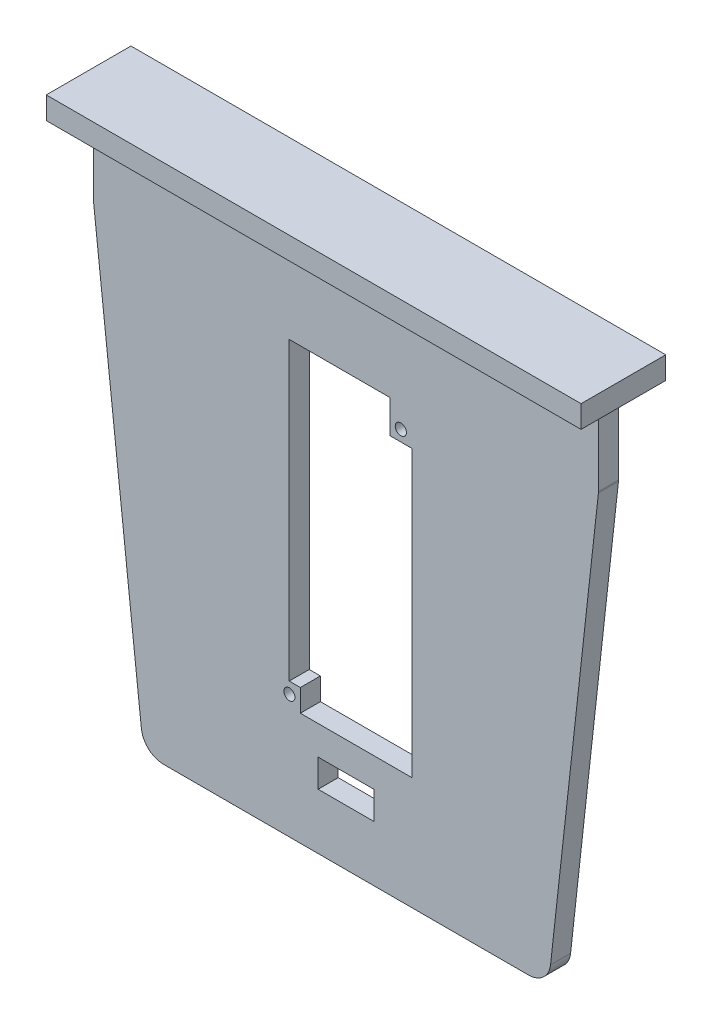
SolidWorks part; units mm, degrees
ref_plane "Front Plane" through (0, 0, 0) normal (0, 0, 1) x (1, 0, 0)
ref_plane "Top Plane" through (0, 0, 0) normal (0, 1, 0) x (1, 0, 0)
ref_plane "Right Plane" through (0, 0, 0) normal (1, 0, 0) x (0, 0, -1)
sketch "Sketch2" plane through (0, 0, 0) normal (0, 0, -1) x (-1, 0, 0)
  line L0 (-4.9216, 54.5793) -> (-4.9216, -59.013) construction
  line L6 (-62.4874, 48.8485) -> (52.6441, 48.8485)
  line L7 (52.6441, 48.8485) -> (41.7132, -49.932)
  line L8 (36.664, -54.4533) -> (-46.5073, -54.4533)
  line L9 (-62.4874, 48.8485) -> (-51.5564, -49.932)
  arc A4 (41.7132, -49.932) -> (36.664, -54.4533) centre (36.664, -49.3733) cw
  arc A5 (-51.5564, -49.932) -> (-46.5073, -54.4533) centre (-46.5073, -49.3733) ccw
  point P27 (-4.9216, -54.4533)
  point P28 (-4.9216, 48.8485)
  dimension "D4" = 98.7805
  dimension "D6" = 48.8485
  dimension "D11" = 5.08
  dimension "D2" = 115.1315
  dimension "D3" = 83.1712
  dimension "D5" = 36.664
extrude "Boss-Extrude1" add sketch "Sketch2" along normal blind 4.572
sketch "Sketch3" plane through (0, 48.8485, 0) normal (0, 1, 0) x (1, 0, 0)
  line L0 (-52.6441, 4.572) -> (-52.6441, 0)
  line L1 (-52.6441, 4.572) -> (62.4874, 4.572)
  line L2 (-52.6441, 0) -> (62.4874, 0)
  line L3 (62.4874, 4.572) -> (62.4874, 0)
  line L4 (62.4874, 4.572) -> (62.4874, 0) construction
  dimension "D1" = 0
extrude "Boss-Extrude2" add sketch "Sketch3" along normal blind 17.78
sketch "Sketch4" plane through (0, 66.6285, 0) normal (0, 1, 0) x (1, 0, 0)
  line L0 (-52.6441, 0) -> (62.4874, 0) construction
  line L1 (62.4874, 0) -> (62.4874, 4.572) construction
  line L2 (-52.6441, 0) -> (62.4874, 0) construction
  line L3 (62.4874, -7.366) -> (62.4874, 11.938) construction
  line L4 (-52.6441, -7.366) -> (-52.6441, 37.8542) construction
  line L5 (0, -33.6753) -> (0, 37.8542) construction
  line L10 (-56.0384, 11.938) -> (-56.0384, -7.366)
  line L11 (-56.0384, 11.938) -> (82.2468, 11.938) construction
  line L12 (62.4874, -7.366) -> (-56.0384, -7.366) construction
  line L13 (-56.0384, 11.938) -> (65.8816, 11.938)
  line L14 (-56.0384, -7.366) -> (65.8816, -7.366)
  line L15 (65.8816, 11.938) -> (65.8816, -7.366)
  line L16 (62.4874, 4.572) -> (-52.6441, 4.572) construction
  dimension "D1" = 7.366
  dimension "D2" = 7.366
  dimension "D3" = 3.3942
  dimension "D4" = 3.3942
fillet "Fillet1" radius 2.54 2 edges at (62.4874, 48.8485, -2.286) (-52.6441, 48.8485, -2.286)
extrude "Boss-Extrude4" add sketch "Sketch4" along normal blind 5.08
sketch "Sketch5" plane through (0, 0, -4.572) normal (0, 0, -1) x (-1, 0, 0)
  line L0 (-4.9216, 66.6285) -> (-4.9216, -54.4533) construction
  line L2 (-65.8816, 66.6285) -> (56.0384, 66.6285) construction
  line L3 (-46.5073, -54.4533) -> (36.664, -54.4533) construction
  line L4 (1.4284, -35.4033) -> (-11.2716, -35.4033)
  line L5 (-11.2716, -35.4033) -> (-11.2716, -41.7533)
  line L6 (-11.2716, -41.7533) -> (1.4284, -41.7533)
  line L7 (1.4284, -35.4033) -> (1.4284, -41.7533)
  point P11 (-4.9216, -41.7533)
  point P12 (-4.9216, -35.4033)
  dimension "D1" = 6.35
  dimension "D2" = 6.35
  dimension "D3" = 12.7
extrude "Cut-Extrude1" cut sketch "Sketch5" against normal blind 5.08
sketch "Sketch6" plane through (0, 0, -4.572) normal (0, 0, -1) x (-1, 0, 0)
  line L0 (-62.4874, 66.6285) -> (-62.4874, 48.9886) construction
  line L1 (-65.8816, 66.6285) -> (56.0384, 66.6285) construction
  line L2 (-11.2716, -41.7533) -> (1.4284, -41.7533) construction
  line L3 (47.9122, 6.0876) -> (-57.7555, 6.0876) construction
  line L4 (-62.4874, 66.6285) -> (52.6441, 66.6285) construction
  line L5 (41.7132, -49.932) -> (52.6287, 48.7092) construction
  line L7 (-62.472, 48.7092) -> (-51.5564, -49.932) construction
  line L8 (-14.9216, 41.2285) -> (-19.9216, 41.2285)
  line L9 (-19.9216, 41.2285) -> (-19.9216, -28.7715)
  line L10 (-19.9216, -28.7715) -> (5.4784, -28.7715)
  line L11 (-19.9216, 41.2285) -> (-19.9216, 36.2285)
  line L12 (-19.9216, 41.2285) -> (-14.9216, 41.2285)
  line L13 (-19.9216, 36.2285) -> (-14.9216, 36.2285)
  line L14 (-14.9216, 41.2285) -> (-14.9216, 36.2285)
  line L15 (-46.5073, -54.4533) -> (36.664, -54.4533) construction
  line L16 (-14.9216, 41.2285) -> (-14.9216, 43.7685)
  line L17 (-14.9216, 43.7685) -> (8.0184, 43.7685)
  line L20 (5.4784, -28.7715) -> (5.4784, -23.6915)
  line L21 (5.4784, -23.6915) -> (8.0184, -23.6915)
  line L22 (-17.4216, 36.2285) -> (-17.4216, 41.2285) construction
  line L23 (-14.9216, 38.7285) -> (-19.9216, 38.7285) construction
  line L24 (8.0184, -23.6915) -> (8.0184, 43.7685)
  circle A0 centre (-17.4216, 38.7285) radius 1.27
  circle A3 centre (7.9784, -26.2715) radius 1.27
  point P19 (-7.2216, -28.7715)
  point P20 (-17.4216, 41.2285)
  dimension "D7" = 2.54
  dimension "D10" = 2.54
  dimension "D11" = 67.46
  dimension "D2" = 2.54
  dimension "D8" = 5.08
  dimension "D16" = 28.1818
  dimension "D1" = 60.5409
  dimension "D3" = 70
  dimension "D4" = 25.4
  dimension "D5" = 5
  dimension "D6" = 5
  dimension "D9" = 42.5504
  dimension "D12" = 2.5
  dimension "D13" = 25.4
  dimension "D17" = 2.54
extrude "Cut-Extrude2" cut sketch "Sketch6" against normal blind 6.35 contours L21 L24 L17 L16 L14 L13 L9 L10 L20 | A0 | A3
